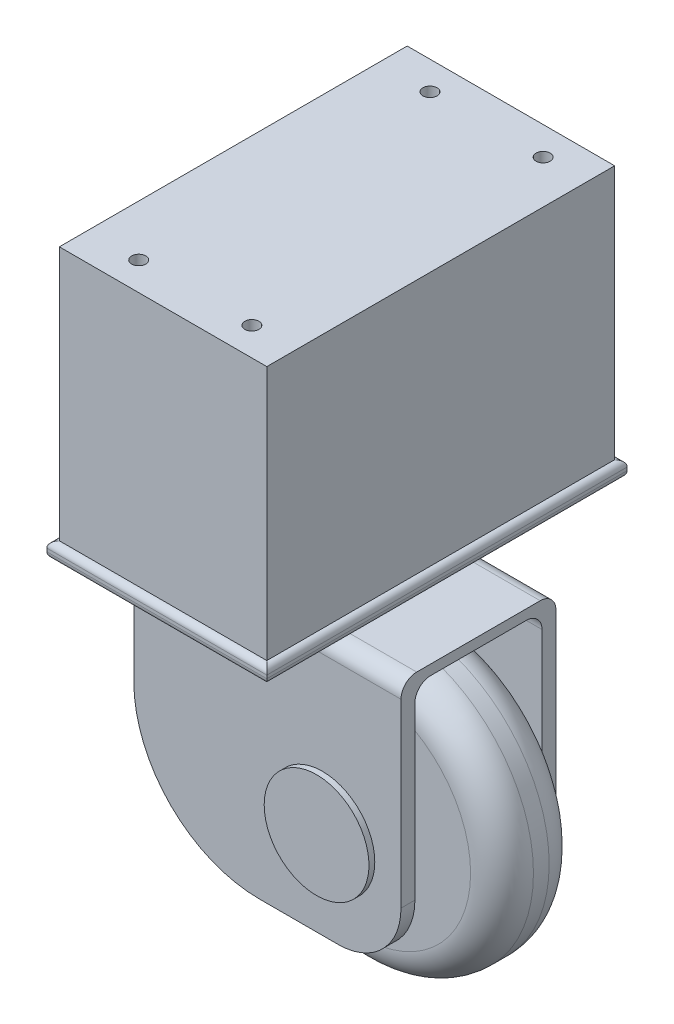
SolidWorks part; units mm, degrees
material "Silicon Rubber"
ref_plane "Front Plane" through (0, 0, 0) normal (0, 0, 1) x (1, 0, 0)
ref_plane "Top Plane" through (0, 0, 0) normal (0, 1, 0) x (1, 0, 0)
ref_plane "Right Plane" through (0, 0, 0) normal (1, 0, 0) x (0, 0, -1)
sketch "Sketch1" plane through (0, 0, 0) normal (0, 0, 1) x (1, 0, 0)
  circle A0 centre (0, 0) radius 45
  dimension "D1" = 90
extrude "Boss-Extrude1" add sketch "Sketch1" along normal blind 25
sketch "Sketch2" plane through (0, 0, 0) normal (1, 0, 0) x (0, 0, -1)
  line L0 (-108.6138, 0) -> (99.872, 0) construction
  line L1 (-12.5, 45) -> (-12.5, -75.6223) construction
  line L2 (0, 45) -> (-25, 45) construction
  line L3 (-32.7112, -28.5528) -> (-32.7112, 50.8)
  line L4 (-32.7112, 50.8) -> (7.7112, 50.8)
  line L6 (12.147, 54.0036) -> (-37.147, 54.0036)
  line L7 (-37.147, 54.0036) -> (-37.147, -28.5528)
  line L8 (-37.147, -28.5528) -> (-32.7112, -28.5528)
  line L9 (12.147, -28.5528) -> (7.7112, -28.5528)
  line L10 (12.147, 54.0036) -> (12.147, -28.5528)
  line L11 (7.7112, -28.5528) -> (7.7112, 50.8)
extrude "Boss-Extrude2" add sketch "Sketch2" along normal blind 25 and the other way blind 60 separate body
sketch "Sketch3" plane through (0, 54.0036, 0) normal (0, 1, 0) x (1, 0, 0)
  line L0 (25, -12.5) -> (-60, -12.5) construction
  line L1 (25, 12.147) -> (25, -37.147) construction
  line L2 (-60, 12.147) -> (-60, -37.147) construction
  circle A0 centre (-20, -13.4189) radius 16.6944
  dimension "D1" = 40
extrude "Boss-Extrude3" add sketch "Sketch3" along normal blind 10
sketch "Sketch4" plane through (0, 64.0036, 0) normal (0, 1, 0) x (1, 0, 0)
  line L1 (-55, 44.83) -> (15, 44.83)
  line L2 (-55, 44.83) -> (-55, -69.83)
  line L3 (-55, -69.83) -> (15, -69.83)
  line L4 (15, 44.83) -> (15, -69.83)
  line L6 (-55, -12.5) -> (25, -12.5) construction
  line L7 (25, 12.147) -> (25, -37.147) construction
  line L8 (-20, -30.1133) -> (-20, 90.3061) construction
  circle A0 centre (-20, -13.4189) radius 16.6944 construction
  circle A1 centre (-20, -13.4189) radius 16.6944 construction
  point P8 (25, -12.5)
  dimension "D1" = 114.66
  dimension "D2" = 70
extrude "Boss-Extrude4" add sketch "Sketch4" along normal blind 5
sketch "Sketch5" plane through (0, 0, 0) normal (0, 0, -1) x (-1, 0, 0)
  circle A0 centre (0, 0) radius 16.6673
extrude "Boss-Extrude5" add sketch "Sketch5" along normal blind 14 and the other way blind 39
fillet "Fillet1" radius 10 2 edges at (45, 0, 25) (45, 0, 0)
fillet "Fillet2" radius 40 2 edges at (-60, -28.5528, 34.9291) (-60, -28.5528, -9.9291)
fillet "Fillet3" radius 20 2 edges at (25, -28.5528, 34.9291) (25, -28.5528, -9.9291)
fillet "Fillet4" radius 5 4 edges at (-17.5, 54.0036, 37.147) (-17.5, 54.0036, -12.147) (-17.5, 50.8, 32.7112) (-17.5, 50.8, -7.7112)
fillet "Fillet5" radius 2 8 edges at (-20, 64.0036, 69.83) (15, 64.0036, 12.5) (-20, 64.0036, -44.83) (-55, 64.0036, 12.5) (-20, 69.0036, -44.83) (15, 69.0036, 12.5) (-20, 69.0036, 69.83) (-55, 69.0036, 12.5)
scale "Scale1" scale about centroid uniform scaling yes scale factor 1.111111
ref_plane "Ground" through (0, -51.8082, 0) normal (0, -1, 0) x (-1, 0, 0)
sketch "Sketch6" plane through (0, 74.8625, 0) normal (0, 1, 0) x (1, 0, 0)
  line L0 (15.275, 48.9809) -> (-58.0583, 48.9809)
  line L1 (15.275, 48.9809) -> (-58.0583, 48.9809) construction
  line L2 (-58.0583, 48.9809) -> (-58.0583, -73.9746)
  line L3 (-58.0583, -73.9746) -> (15.275, -73.9746)
  line L4 (15.275, -73.9746) -> (15.275, 48.9809)
extrude "Boss-Extrude6" add sketch "Sketch6" along normal blind 90
sketch "Sketch7" plane through (0, 164.8625, 0) normal (0, 1, 0) x (1, 0, 0)
  line L0 (15.275, 48.9809) -> (-58.0583, 48.9809) construction
  line L1 (-58.0583, -73.9746) -> (15.275, -73.9746) construction
  circle A0 centre (0, 38.9809) radius 2.5
  circle A1 centre (-40, 38.9809) radius 2.5
  circle A2 centre (0, -63.9746) radius 2.5
  circle A3 centre (-40, -63.9746) radius 2.5
  point P8 (0, 0)
  point P13 (0, 0)
  dimension "D1" = 5
  dimension "D2" = 5
  dimension "D3" = 5
  dimension "D4" = 5
  dimension "D5" = 10
  dimension "D6" = 10
  dimension "D7" = 10
  dimension "D8" = 10
  dimension "D9" = 40
  dimension "D10" = 40
extrude "Cut-Extrude1" cut sketch "Sketch7" against normal through all both and the other way through all
